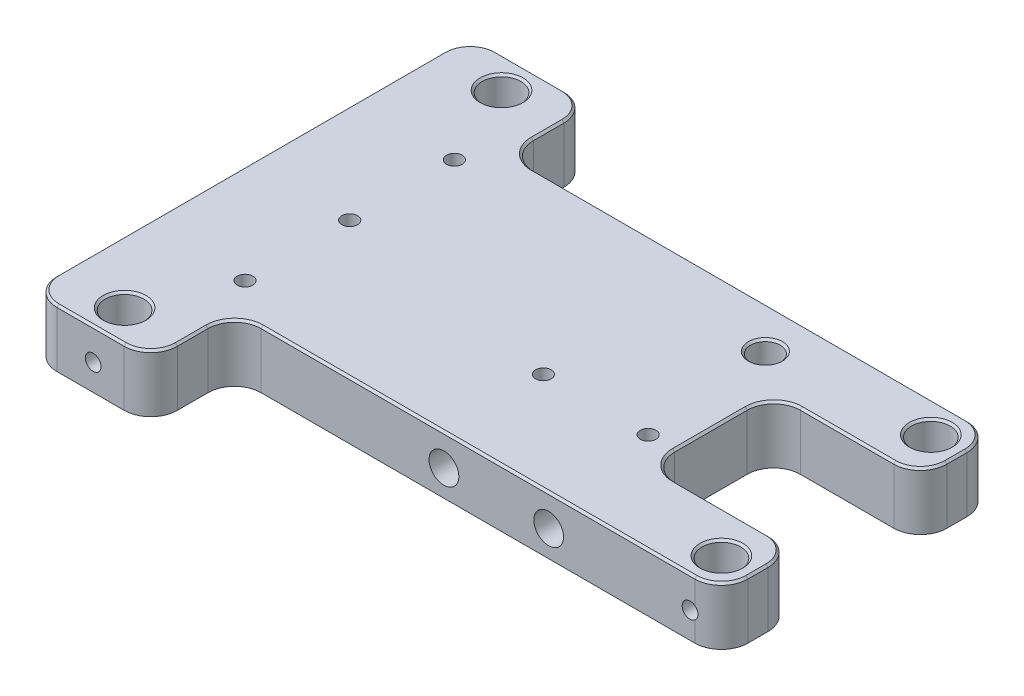
SolidWorks part; units mm, degrees
material "6061-T6 (SS)"
ref_plane "Front" through (0, 0, 0) normal (0, 0, 1) x (1, 0, 0)
ref_plane "Top" through (0, 0, 0) normal (0, 1, 0) x (1, 0, 0)
ref_plane "Right" through (0, 0, 0) normal (1, 0, 0) x (0, 0, -1)
sketch "Sketch1" plane through (0, 0, 0) normal (0, 1, 0) x (1, 0, 0)
  line L1 (-58, 42) -> (0, 42)
  line L2 (-58, 42) -> (-58, 0)
  line L3 (-58, 0) -> (0, 0)
  line L4 (0, 42) -> (0, 0)
  dimension "D1" = 58
  dimension "D2" = 42
extrude "Extrude1" add sketch "Sketch1" along normal blind 5.5
ref_plane "Plane1" through (0, 0, -21) normal (0, 0, -1) x (-1, 0, 0)
sketch "Sketch2" plane through (0, 5.5, 0) normal (0, 1, 0) x (1, 0, 0)
  line L0 (0, 0) -> (0, 42) construction
  line L1 (0, 27) -> (-14, 27)
  line L2 (0, 27) -> (0, 15)
  line L3 (0, 15) -> (-14, 15)
  line L4 (-14, 27) -> (-14, 15)
  line L5 (3.025, 21) -> (-3.025, 21) construction
  dimension "D1" = 6
  dimension "D2" = 6
  dimension "D3" = 14
extrude "Extrude2" cut sketch "Sketch2" against normal through all
sketch "Sketch3" plane through (0, 5.5, 0) normal (0, 1, 0) x (1, 0, 0)
  line L0 (3.025, 21) -> (-3.025, 21) construction
  line L1 (0, 42) -> (-46.5, 42)
  line L2 (0, 42) -> (0, 34)
  line L3 (0, 34) -> (-46.5, 34)
  line L4 (-46.5, 42) -> (-46.5, 34)
  dimension "D1" = 11.5
  dimension "D2" = 13
extrude "Extrude3" cut sketch "Sketch3" against normal through all
sketch "Sketch4" plane through (0, 5.5, 0) normal (0, 1, 0) x (1, 0, 0)
  line L0 (-58, 42) -> (-58, 0) construction
  line L1 (3.025, 21) -> (-3.025, 21) construction
  circle A0 centre (-52, 39) radius 1.85
  circle A1 centre (-3, 31) radius 1.85
  dimension "D1" = 3.7
  dimension "D2" = 3.7
  dimension "D3" = 6
  dimension "D4" = 18
  dimension "D5" = 10
  dimension "D6" = 49
extrude "Extrude4" cut sketch "Sketch4" against normal through all
mirror "Mirror2" about plane through (0, 0, -21) normal (0, 0, -1) of "Extrude4", "Extrude3"
fillet "Fillet2" radius 2.54 12 edges at (-58, 2.75, -42) (-46.5, 2.75, -34) (-14, 2.75, -15) (-46.5, 2.75, -42) (0, 2.75, -34) (0, 2.75, -27) (-14, 2.75, -27) (0, 2.75, -15) (0, 2.75, -8) (-46.5, 2.75, -8) (-46.5, 2.75, 0) (-58, 2.75, 0)
hole_wizard "#4-40 Tapped Hole1" positions "3DSketch1" profile "Sketch5" tap size "#4-40" standard "Ansi Inch"
sketch3d "3DSketch1"
  line L0 (-58, 5.5, -39.46) -> (-58, 5.5, -2.54) construction
  point P0 (-17.8, 5.5, -30)
  dimension "D1" = 9
  dimension "D2" = 40.2
sketch "Sketch5" plane through (-17.8, 5.5, -30) normal (1, 0, 0) x (0, 0, 1)
  line L0 (0, 0) -> (0, 10.8142)
  line L1 (0, 10.8142) -> (1.1303, 10.135)
  line L2 (1.1303, 10.135) -> (1.1303, 8.23)
  line L3 (1.1303, 8.23) -> (1.4224, 8.23)
  line L4 (1.4224, 8.23) -> (1.4224, 0)
  line L5 (1.4224, 0) -> (0, 0)
  line L10 (0, 10.8142) -> (-1.1303, 10.135) construction
  line L11 (0, -6.35) -> (0, 107.95) construction
  dimension "Tap Drill Dia." = 2.2606
  dimension "Tap Drill Depth" = 10.135
  dimension "Thread Major Dia." = 2.8448
  dimension "Thread Depth" = 8.23
  dimension "Drill Angle" = 118
chamfer "Chamfer1" distance 0.2 angle 45 29 edges at (-3, 5.5, -12.85) (-47.2439, 5.5, -41.2561) (-46.5, 5.5, -38) (-45.7561, 5.5, -34.7439) (-23.25, 5.5, -34) (-0.7439, 5.5, -33.2561) (0, 5.5, -30.5) (-0.7439, 5.5, -27.7439) (-7, 5.5, -27) (-13.2561, 5.5, -26.2561) (-14, 5.5, -21) (-13.2561, 5.5, -15.7439) (-7, 5.5, -15) (-0.7439, 5.5, -14.2561) (0, 5.5, -11.5) (-0.7439, 5.5, -8.7439) (-23.25, 5.5, -8) (-45.7561, 5.5, -7.2561) (-46.5, 5.5, -4) (-47.2439, 5.5, -0.7439) (-52.25, 5.5, 0) (-57.2561, 5.5, -0.7439) (-58, 5.5, -21) (-57.2561, 5.5, -41.2561) (-52.25, 5.5, -42) (-3, 5.5, -29.15) (-52, 5.5, -37.15) (-52, 5.5, -4.85) (-17.8, 5.5, -28.5776)
sketch "Sketch6" plane through (-58, 0, 0) normal (-1, 0, 0) x (0, 0, 1)
  line L0 (-39.46, 0) -> (-2.54, 0) construction
  line L1 (-39.46, 0) -> (-2.54, 0)
  line L2 (-39.46, 0) -> (-39.46, 0.5)
  line L3 (-39.46, 0.5) -> (-2.54, 0.5)
  line L4 (-2.54, 0) -> (-2.54, 0.5)
  line L6 (-39.46, 5.3) -> (-39.46, 0) construction
  line L7 (-2.54, 0) -> (-2.54, 5.3) construction
  dimension "D3" = 0.5
extrude "Extrude5" add sketch "Sketch6" along normal blind 1
hole_wizard "#4-40 Tapped Hole2" positions "3DSketch2" profile "Sketch7" tap size "#4-40" standard "Ansi Inch"
sketch3d "3DSketch2"
  line L1 (-43.96, 0, -8) -> (-2.54, 0, -8) construction
  line L2 (-58, 0.5, -2.54) -> (-58, 0.5, -39.46) construction
  point P0 (-16.5, 2.5, -8)
  point P2 (-26.5, 2.5, -8)
  point P4 (-58, 3, -11)
  point P6 (-58, 3, -21)
  point P8 (-58, 3, -31)
  dimension "D1" = 31.5
  dimension "D2" = 10
  dimension "D3" = 2.5
  dimension "D4" = 2.5
  dimension "D5" = 10
  dimension "D6" = 10
sketch "Sketch7" plane through (-16.5, 2.5, -8) normal (1, 0, 0) x (0, -1, 0)
  line L0 (0, 0) -> (0, 10.2042)
  line L1 (0, 10.2042) -> (1.1303, 9.525)
  line L2 (1.1303, 9.525) -> (1.1303, 8.2296)
  line L3 (1.1303, 8.2296) -> (1.4224, 8.2296)
  line L4 (1.4224, 8.2296) -> (1.4224, 0)
  line L5 (1.4224, 0) -> (0, 0)
  line L10 (0, 10.2042) -> (-1.1303, 9.525) construction
  line L11 (0, -6.35) -> (0, 107.95) construction
  dimension "Tap Drill Dia." = 2.2606
  dimension "Tap Drill Depth" = 9.525
  dimension "Thread Major Dia." = 2.8448
  dimension "Thread Depth" = 8.2296
  dimension "Drill Angle" = 118
sketch "Sketch8" plane through (0, 5.5, 0) normal (0, 1, 0) x (1, 0, 0)
  line L0 (3.025, 21) -> (-3.025, 21) construction
  line L1 (-2.54, 8) -> (-43.96, 8) construction
  line L2 (-58, 2.54) -> (-58, 39.46) construction
  circle A0 centre (-48.5, 31) radius 0.75
  circle A1 centre (-48.5, 21) radius 0.75
  circle A2 centre (-48.5, 11) radius 0.75
  circle A3 centre (-26.5, 17.5) radius 0.75
  circle A4 centre (-16.5, 17.5) radius 0.75
  dimension "D1" = 1.5
  dimension "D2" = 1.5
  dimension "D3" = 1.5
  dimension "D4" = 1.5
  dimension "D5" = 1.5
  dimension "D6" = 9.5
  dimension "D7" = 9.5
  dimension "D8" = 31.5
  dimension "D9" = 10
  dimension "D10" = 10
  dimension "D11" = 10
extrude "Extrude6" cut sketch "Sketch8" against normal blind 2.5
sketch "Sketch9" plane through (0, 0, -8) normal (0, 0, 1) x (1, 0, 0)
  line L1 (-43.96, 0) -> (-2.54, 0) construction
  line L2 (-58, 0.5) -> (-58, 5.3) construction
  circle A1 centre (-3, 2.5) radius 0.75
  dimension "D1" = 1.5
  dimension "D2" = 2.5
  dimension "D3" = 55
extrude "Extrude7" cut sketch "Sketch9" against normal blind 2.5
sketch "Sketch10" plane through (0, 0, 0) normal (0, 0, 1) x (1, 0, 0)
  line L0 (-58, 0.5) -> (-58, 5.3) construction
  line L1 (-55.46, 0) -> (-49.04, 0) construction
  circle A0 centre (-52, 2.5) radius 0.75
  dimension "D1" = 1.5
  dimension "D2" = 6
  dimension "D3" = 2.5
extrude "Extrude8" cut sketch "Sketch10" against normal blind 2.5
mirror "Mirror3" about plane through (0, 0, -21) normal (0, 0, -1) of "Extrude8", "Extrude7"
equation "\"D2@Sketch4\" = \"D1@Sketch4\""
